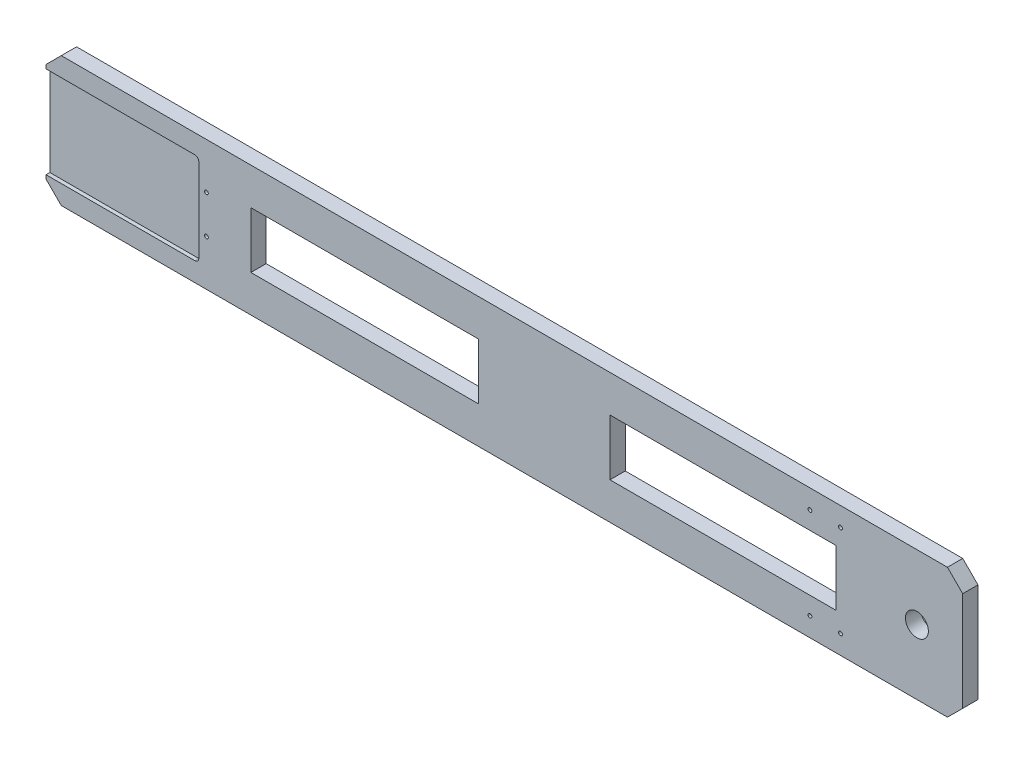
SolidWorks part; units mm, degrees
ref_plane "前视基准面" through (0, 0, 0) normal (0, 0, 1) x (1, 0, 0)
ref_plane "上视基准面" through (0, 0, 0) normal (0, 1, 0) x (1, 0, 0)
ref_plane "右视基准面" through (0, 0, 0) normal (1, 0, 0) x (0, 0, -1)
sketch "草图1" plane through (0, 0, 0) normal (0, 0, 1) x (1, 0, 0)
  line L0 (-580, 85) -> (-600, 65)
  line L1 (580, -85) -> (-580, -85)
  line L2 (600, -65) -> (600, 65)
  line L3 (580, 85) -> (-580, 85)
  line L4 (-600, -65) -> (-600, 65)
  line L5 (600, -85) -> (-600, 85) construction
  line L6 (600, 85) -> (-600, -85) construction
  line L7 (-580, -85) -> (-600, -65)
  line L8 (600, 65) -> (580, 85)
  line L9 (600, -65) -> (580, -85)
  point P0 (0, 0)
  dimension "D1" = 170
  dimension "D2" = 1200
extrude "凸台-拉伸1" add sketch "草图1" along normal blind 20
sketch "草图2" plane through (0, 0, 20) normal (0, 0, 1) x (1, 0, 0)
  line L0 (600, 0) -> (540, 0) construction
  line L1 (600, -65) -> (600, 65) construction
  circle A0 centre (540, 0) radius 15
  dimension "D1" = 30
  dimension "D2" = 60
extrude "切除-拉伸1" cut sketch "草图2" against normal through all
sketch "草图3" plane through (0, 0, 20) normal (0, 0, 1) x (1, 0, 0)
  line L0 (-600, 65) -> (-600, -65) construction
  line L1 (-800, -60) -> (-405, -60)
  line L2 (-800, -60) -> (-800, 60)
  line L3 (-800, 60) -> (-405, 60)
  line L4 (-400, -55) -> (-400, 55)
  line L5 (-800, -60) -> (-400, 60) construction
  line L6 (-800, 60) -> (-400, -60) construction
  arc A0 (-405, -60) -> (-400, -55) centre (-405, -55) ccw
  arc A1 (-405, 60) -> (-400, 55) centre (-405, 55) cw
  point P0 (-600, 0)
  dimension "D3" = 5
  dimension "D1" = 200
  dimension "D2" = 120
extrude "切除-拉伸2" cut sketch "草图3" against normal blind 5
sketch "草图9" plane through (0, 0, 20) normal (0, 0, 1) x (1, 0, 0)
  line L1 (525, -70) -> (-525, -70)
  line L2 (525, -70) -> (525, 70)
  line L3 (525, 70) -> (-525, 70)
  line L4 (-525, -70) -> (-525, 70)
  line L5 (525, -70) -> (-525, 70) construction
  line L6 (525, 70) -> (-525, -70) construction
  line L7 (325, -70) -> (-325, -70)
  line L8 (325, -70) -> (325, 70)
  line L9 (325, 70) -> (-325, 70)
  line L10 (-325, -70) -> (-325, 70)
  line L11 (325, -70) -> (-325, 70) construction
  line L12 (325, 70) -> (-325, -70) construction
  point P0 (0, 0)
  point P5 (0, 0)
  dimension "D1" = 140
  dimension "D2" = 1050
  dimension "D3" = 650
sketch "草图11" plane through (0, 0, 20) normal (0, 0, 1) x (1, 0, 0)
  line L0 (-400, 0) -> (-390, 0) construction
  line L1 (-400, -55) -> (-400, 55) construction
  line L2 (-390, 0) -> (-390, 25) construction
  circle A0 centre (-390, 25) radius 7.7911
  circle A1 centre (-390, -25) radius 7.7911
  dimension "D1" = 50
  dimension "D2" = 10
hole_wizard "M6 螺纹孔1" positions "3D草图2" profile "草图12" tap size "M6" standard "Iso"
sketch3d "3D草图2"
  point P0 (-390, 25, 20)
  point P3 (-390, -25, 20)
sketch "草图12" plane through (-390, 25, 20) normal (1, 0, 0) x (0, -1, 0)
  line L0 (0, 0) -> (0, 16.5022)
  line L1 (0, 16.5022) -> (2.5, 15)
  line L2 (2.5, 15) -> (2.5, 0)
  line L5 (2.5, 0) -> (0, 0)
  line L10 (0, 16.5022) -> (-2.5, 15) construction
  line L11 (0, -6.35) -> (0, 107.95) construction
  dimension "螺纹孔钻头直径" = 5
  dimension "螺纹孔钻头深度" = 15
  dimension "导头角度" = 118
sketch "草图13" plane through (0, 0, 20) normal (0, 0, 1) x (1, 0, 0)
  line L0 (-431.4416, -85) -> (-431.4416, -65) construction
  line L1 (-580, -85) -> (580, -85) construction
  line L2 (-431.4416, -65) -> (-451.4416, -65) construction
  line L3 (0, 0) -> (0, -166.8896) construction
  circle A0 centre (-451.4416, -65) radius 5.1126
  circle A1 centre (-411.4416, -65) radius 5.1126
  circle A2 centre (411.4416, -65) radius 5.1126
  circle A3 centre (451.4416, -65) radius 5.1126
  dimension "D1" = 40
  dimension "D2" = 20
sketch "草图15" plane through (0, 0, 20) normal (0, 0, 1) x (1, 0, 0)
  line L0 (420, 85) -> (420, 60) construction
  line L1 (420, 60) -> (400, 60) construction
  line L2 (580, 85) -> (-580, 85) construction
  line L3 (600, -65) -> (600, 65) construction
  circle A0 centre (400, 60) radius 8.5198
  circle A1 centre (440, 60) radius 8.5198
  dimension "D1" = 40
  dimension "D2" = 180
  dimension "D3" = 25
hole_wizard "M6 螺纹孔2" positions "3D草图4" profile "草图16" tap size "M6" standard "Iso"
sketch3d "3D草图4"
  point P0 (400, 60, 20)
  point P3 (440, 60, 20)
sketch "草图16" plane through (400, 60, 20) normal (1, 0, 0) x (0, -1, 0)
  line L0 (0, 0) -> (0, 16.5022)
  line L1 (0, 16.5022) -> (2.5, 15)
  line L2 (2.5, 15) -> (2.5, 0)
  line L5 (2.5, 0) -> (0, 0)
  line L10 (0, 16.5022) -> (-2.5, 15) construction
  line L11 (0, -6.35) -> (0, 107.95) construction
  dimension "螺纹孔钻头直径" = 5
  dimension "螺纹孔钻头深度" = 15
  dimension "导头角度" = 118
mirror "镜向2" about plane through (0, 0, 0) normal (0, 1, 0) of "M6 螺纹孔2"
hole_wizard "大小mm 暗销孔1" positions "草图18" profile "草图17" hole size "Ø12.0" standard "GB"
sketch "草图18" plane through (0, 0, 0) normal (0, 0, -1) x (-1, 0, 0)
  line L0 (-600, 0) -> (600, 0) construction
  line L1 (-600, -65) -> (-600, 65) construction
  line L2 (600, 65) -> (600, -65) construction
  line L5 (0, 85) -> (0, -85) construction
  line L6 (-580, 85) -> (580, 85) construction
  line L7 (580, -85) -> (-580, -85) construction
  point P0 (-250, 65)
  point P2 (250, 65)
  point P4 (250, -65)
  point P6 (-250, -65)
  dimension "D1" = 130
  dimension "D2" = 500
sketch "草图17" plane through (250, 65, 0) normal (1, 0, 0) x (0, 1, 0)
  line L0 (0, 0) -> (0, 5.6052)
  line L1 (0, 5.6052) -> (6, 2)
  line L2 (6, 2) -> (6, 0)
  line L5 (6, 0) -> (0, 0)
  line L10 (0, 5.6052) -> (-6, 2) construction
  line L11 (0, -6.35) -> (0, 107.95) construction
  dimension "孔直径" = 12
  dimension "孔深度" = 2
  dimension "导头角度" = 118
sketch "草图19" plane through (0, 0, 20) normal (0, 0, 1) x (1, 0, 0)
  line L1 (-33.5594, -36.7417) -> (-331.8159, -36.7417)
  line L2 (-33.5594, -36.7417) -> (-33.5594, 36.7417)
  line L3 (-33.5594, 36.7417) -> (-331.8159, 36.7417)
  line L4 (-331.8159, -36.7417) -> (-331.8159, 36.7417)
  line L5 (-33.5594, -36.7417) -> (-331.8159, 36.7417) construction
  line L6 (-33.5594, 36.7417) -> (-331.8159, -36.7417) construction
  line L7 (434.3575, -36.7417) -> (138.2623, -36.7417)
  line L8 (434.3575, -36.7417) -> (434.3575, 36.7417)
  line L9 (434.3575, 36.7417) -> (138.2623, 36.7417)
  line L10 (138.2623, -36.7417) -> (138.2623, 36.7417)
  line L11 (434.3575, -36.7417) -> (138.2623, 36.7417) construction
  line L12 (434.3575, 36.7417) -> (138.2623, -36.7417) construction
  point P0 (-182.6877, 0)
  point P5 (286.3099, 0)
extrude "切除-拉伸3" cut sketch "草图19" against normal through all
